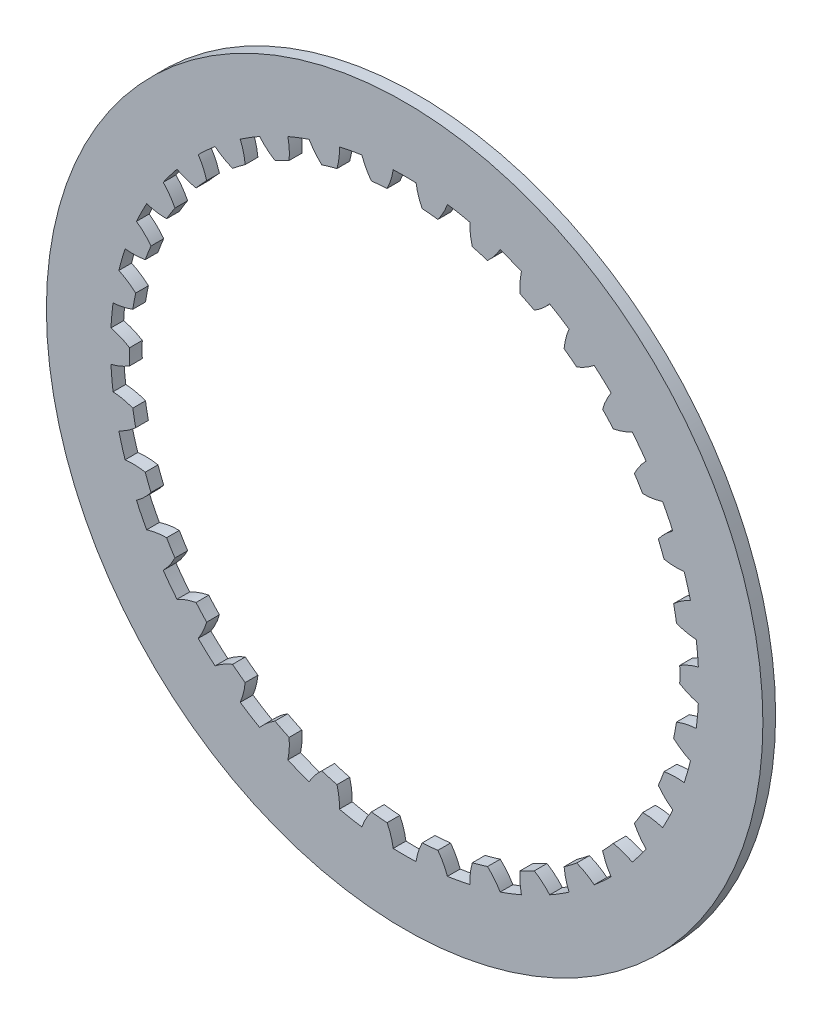
SolidWorks part; units mm, degrees
ref_plane "Front Plane" through (0, 0, 0) normal (0, 0, 1) x (1, 0, 0)
ref_plane "Top Plane" through (0, 0, 0) normal (0, 1, 0) x (1, 0, 0)
ref_plane "Right Plane" through (0, 0, 0) normal (1, 0, 0) x (0, 0, -1)
sketch "Sketch9" plane through (0, 0, 0) normal (0, 0, 1) x (1, 0, 0)
  circle A0 centre (0, 0) radius 54.92
  dimension "D1" = 109.84
extrude "Boss-Extrude7" add sketch "Sketch9" along normal blind 1.95
sketch "Sketch10" plane through (0, 0, 1.95) normal (0, 0, 1) x (1, 0, 0)
  line L0 (0, 0) -> (0, 50000) construction
  line L1 (0, 0) -> (50000, 0) construction
  line L2 (0, 0) -> (17101.0072, 46984.631) construction
  line L3 (0, 0) -> (-17101.0072, 46984.631) construction
  circle A0 centre (0, 0) radius 45.085
  circle A1 centre (0, 0) radius 42.185
  arc A2 (-1.75, 45.051) -> (-2.685, 42.0995) centre (-11.6357, 46.5588) cw
  arc A3 (1.75, 45.051) -> (2.685, 42.0995) centre (11.6357, 46.5588) ccw
  arc A4 (-1.75, 45.051) -> (1.75, 45.051) centre (0, 0) cw
  arc A5 (-2.685, 42.0995) -> (2.685, 42.0995) centre (0, 0) cw
  dimension "D1" = 90.17
  dimension "D2" = 84.37
  dimension "D7" = 10
  dimension "D3" = 20
  dimension "D4" = 20
  dimension "D5" = 5.37
  dimension "D6" = 3.5
extrude "Cut-Extrude3" cut sketch "Sketch10" against normal through all contours A2 A5 A3 A4
pattern_circular "CirPattern1" count 34 over 360 about axis through (0, 0, 0) along (0, 0, 1) of "Cut-Extrude3"
sketch "Sketch12" plane through (0, 0, 1.95) normal (0, 0, 1) x (1, 0, 0)
  circle A0 centre (0, 0) radius 42.185
extrude "Cut-Extrude4" cut sketch "Sketch12" against normal through all
